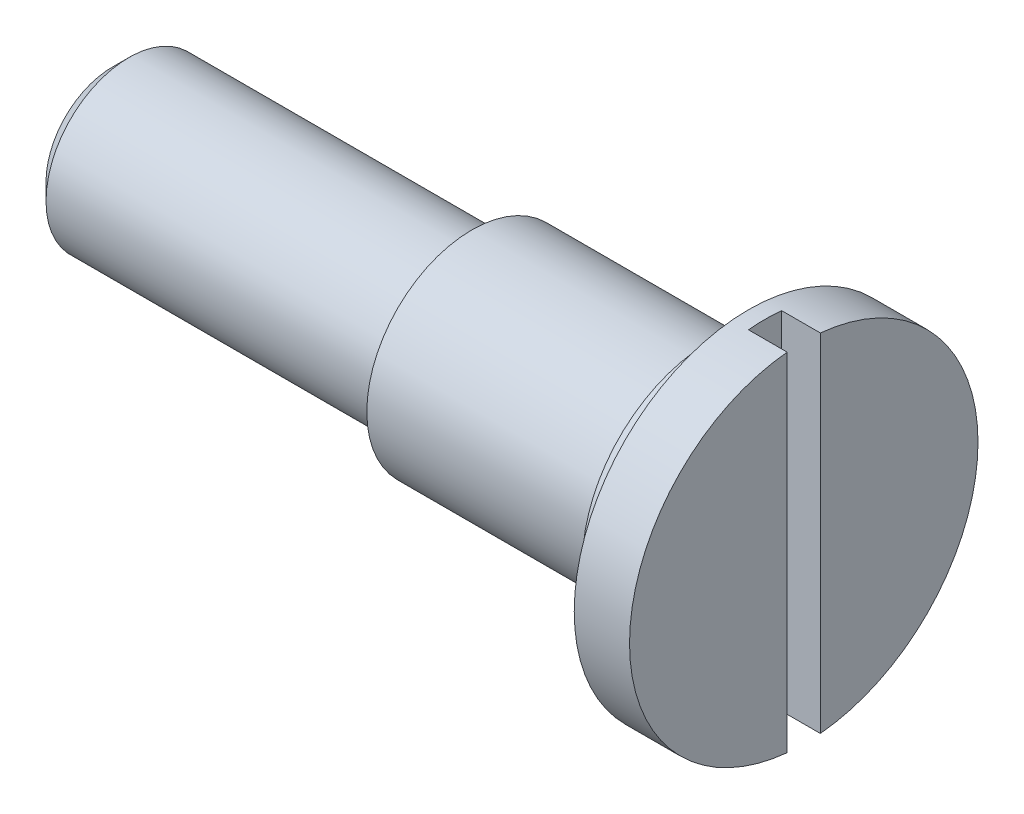
SolidWorks part; units mm, degrees
ref_plane "Спереди" through (0, 0, 0) normal (0, 0, 1) x (1, 0, 0)
ref_plane "Сверху" through (0, 0, 0) normal (0, 1, 0) x (1, 0, 0)
ref_plane "Справа" through (0, 0, 0) normal (1, 0, 0) x (0, 0, -1)
sketch "Эскиз1" plane through (0, 0, 0) normal (0, 1, 0) x (1, 0, 0)
  line L0 (0, 0) -> (0, 1.2)
  line L1 (0.3, 1.5) -> (6.5, 1.5)
  line L2 (6.5, 1.5) -> (6.5, 1.9)
  line L3 (6.5, 1.9) -> (10.8, 1.9)
  line L4 (11.5, 3.15) -> (11.5, 2.3)
  line L5 (11.5, 3.15) -> (12.5, 3.15)
  line L6 (12.5, 3.15) -> (12.5, 0)
  line L7 (0, 0) -> (12.5, 0)
  line L8 (-1.8423, 0) -> (16.4039, 0) construction
  line L9 (11.5, 2.3) -> (10.8, 2.3)
  line L10 (10.8, 2.3) -> (10.8, 1.9)
  line L11 (0, 1.2) -> (0.3, 1.5)
  point P1 (0, 1.5)
  dimension "D1" = 3
  dimension "D2" = 3.8
  dimension "D3" = 6.3
  dimension "D4" = 6.5
  dimension "D5" = 4.6
  dimension "D6" = 0.7
  dimension "D7" = 1
  dimension "D8" = 5
  dimension "D11" = 0.3
revolve "Повернуть1" add sketch "Эскиз1" angle 360 about L8
cosmetic thread "Условное изображение резьбы1" parameters "D2"=2.439
sketch "Эскиз2" plane through (0, 0, 0) normal (0, 1, 0) x (1, 0, 0)
  line L0 (12.5, 0.3) -> (11.8, 0.3)
  line L1 (12.5, -3.15) -> (12.5, 3.15) construction
  line L2 (11.8, 0.3) -> (11.8, -0.3)
  line L3 (11.8, -0.3) -> (12.5, -0.3)
  point P4 (11.8, 0)
  dimension "D1" = 0.6
  dimension "D2" = 0.7
extrude "Вырез-Вытянуть1" cut sketch "Эскиз2" against normal through all and the other way through all
